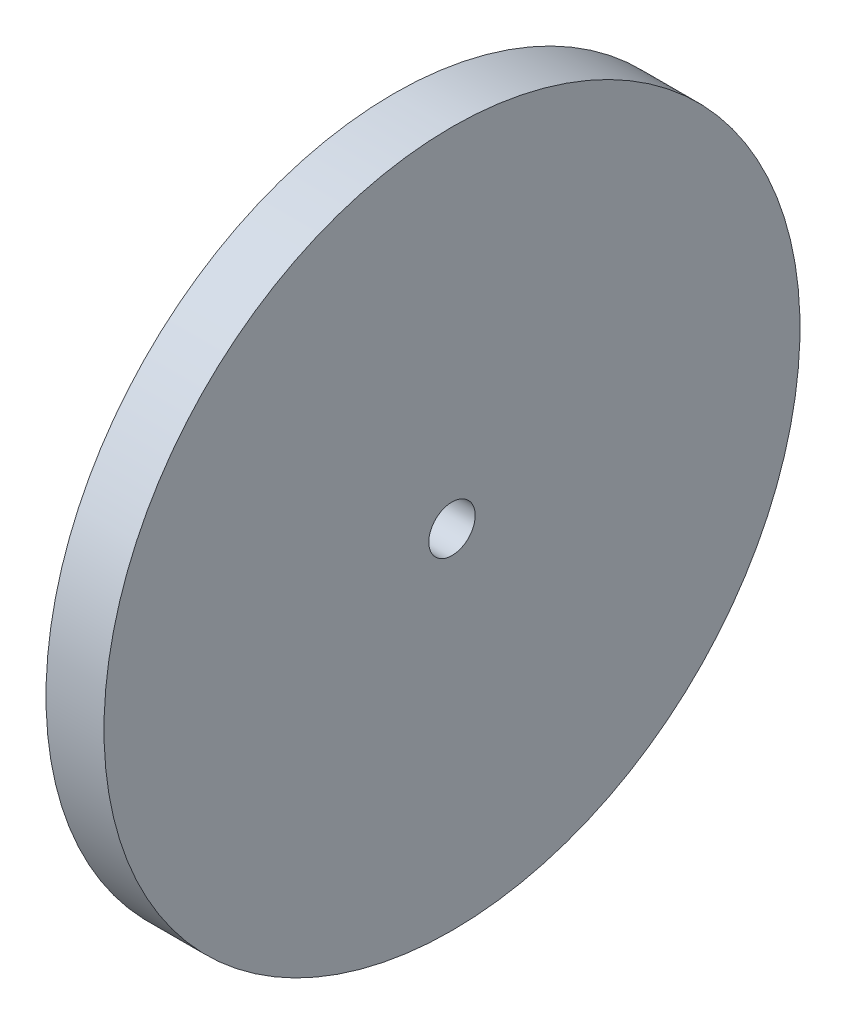
SolidWorks part; units mm, degrees
ref_plane "Front Plane" through (0, 0, 0) normal (0, 0, 1) x (1, 0, 0)
ref_plane "Top Plane" through (0, 0, 0) normal (0, 1, 0) x (1, 0, 0)
ref_plane "Right Plane" through (0, 0, 0) normal (1, 0, 0) x (0, 0, -1)
sketch "Sketch1" plane through (0, 0, 0) normal (0, 0, 1) x (1, 0, 0)
  line L0 (-12.5, 0) -> (12.5, 0)
  line L5 (-12.5, 15) -> (12.5, 15)
  line L10 (12.5, 15) -> (12.5, 0)
  line L14 (-12.5, 15) -> (-12.5, 0)
  arc A1 (-10, 15) -> (10, 15) centre (0, 15) ccw
  point P3 (0, 0)
  dimension "D3" = 10
  dimension "D1" = 15
  dimension "D2" = 25
revolve "Revolve1" add sketch "Sketch1" angle 360 about L0
sketch "Sketch2" plane through (12.5, 0, 0) normal (1, 0, 0) x (0, 0, -1)
  line L0 (0, 37.5) -> (0, -37.5) construction
  circle A1 centre (0, 0) radius 1
  dimension "D1" = 2
extrude "Cut-Extrude1" cut sketch "Sketch2" against normal through all
sketch "Sketch3" plane through (12.5, 0, 0) normal (1, 0, 0) x (0, 0, -1)
  circle A0 centre (0, 0) radius 15
  circle A1 centre (0, 0) radius 15 construction
extrude "Cut-Extrude2" cut sketch "Sketch3" against normal blind 22.5
